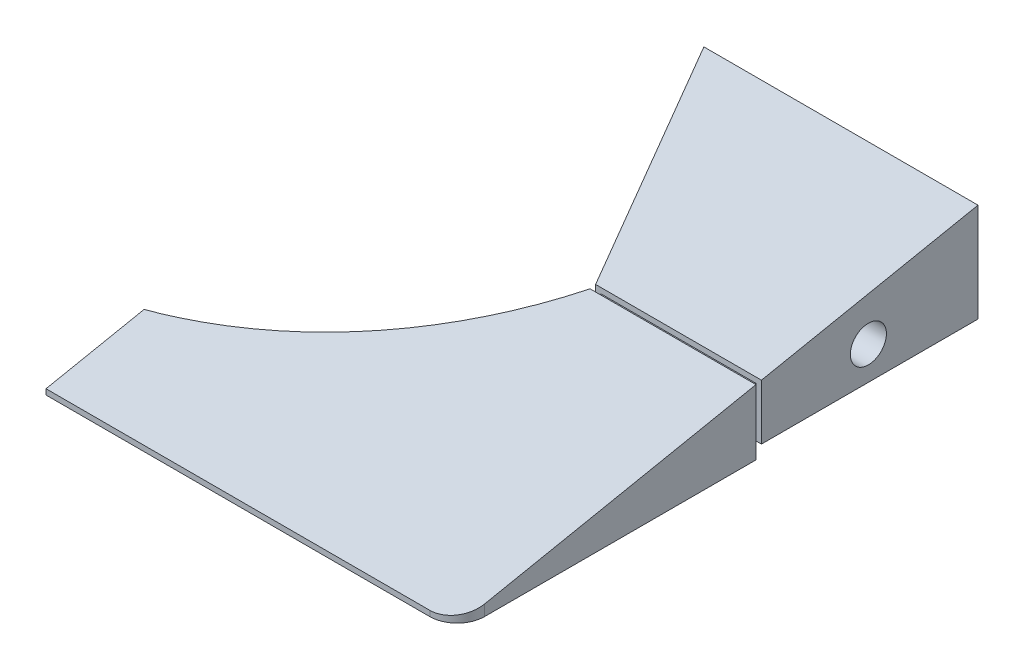
SolidWorks part; units mm, degrees
material "AISI 1020"
ref_plane "Plano frontal" through (0, 0, 0) normal (0, 0, 1) x (1, 0, 0)
ref_plane "Plano superior" through (0, 0, 0) normal (0, 1, 0) x (1, 0, 0)
ref_plane "Plano direito" through (0, 0, 0) normal (1, 0, 0) x (0, 0, -1)
sketch "Esboço1" plane through (0, 0, 0) normal (0, 0, 1) x (1, 0, 0)
  line L1 (-65, 10) -> (65, 10)
  line L2 (-65, 10) -> (-65, -10)
  line L3 (-65, -10) -> (65, -10)
  line L4 (65, 10) -> (65, -10)
  line L5 (-65, 10) -> (65, -10) construction
  line L6 (-65, -10) -> (65, 10) construction
  point P0 (0, 0)
  dimension "D1" = 130
  dimension "D2" = 20
extrude "Ressalto-extrusão1" add sketch "Esboço1" along normal blind 95
sketch "Esboço2" plane through (0, 10, 0) normal (0, 1, 0) x (1, 0, 0)
  line L0 (15, 0) -> (-65, 0)
  line L2 (65, -95) -> (65, 0) construction
  line L3 (35, -40) -> (15, 0)
  line L8 (65, 0) -> (-65, 0) construction
  line L10 (-65, -80) -> (-30.4, -80)
  line L11 (-65, -95) -> (-65, 0) construction
  line L12 (-65, 0) -> (-65, -80)
  arc A0 (-30.4, -80) -> (35, -40) centre (-30.4034, -6.53) ccw
  dimension "D3" = 15
  dimension "D5" = 73.47
  dimension "D1" = 50
  dimension "D2" = 30
  dimension "D4" = 40
extrude "Corte-extrusão2" cut sketch "Esboço2" against normal up to next contours A0 L3 L0 L12 L10
sketch "Esboço3" plane through (65, 0, 0) normal (1, 0, 0) x (0, 0, -1)
  line L0 (0, 10) -> (-95, -9)
  line L1 (-95, -10) -> (-95, 10) construction
  dimension "D1" = 1
extrude "Corte-extrusão3" cut sketch "Esboço3" against normal through all and the other way through all flip side to cut
hole_wizard "Broca de rosquear de cano para tarraxa de 1/82" positions "Esboço7" profile "Esboço8" hole size "1/8" standard "Ansi Inch"
sketch "Esboço7" plane through (65, 0, 0) normal (1, 0, 0) x (0, 0, -1)
  line L0 (0, -10) -> (0, 10) construction
  line L1 (-95, -10) -> (0, -10) construction
  point P0 (-20, -1.945)
  dimension "D1" = 20
  dimension "D2" = 8.055
sketch "Esboço8" plane through (65, -1.945, 20) normal (0, 1, 0) x (0, 0, -1)
  line L0 (0, 0) -> (0, 11.9768)
  line L1 (0, 11.9768) -> (3.29, 10)
  line L2 (3.29, 10) -> (3.29, 0)
  line L5 (3.29, 0) -> (0, 0)
  line L10 (0, 11.9768) -> (-3.29, 10) construction
  line L11 (0, -6.35) -> (0, 107.95) construction
  dimension "Hole Dia." = 6.58
  dimension "Hole Depth" = 10
  dimension "Drill Angle" = 118
hole_wizard "Broca de rosquear de cano para tarraxa de 1/83" positions "Esboço10" profile "Esboço11" hole size "1/8" standard "Ansi Inch"
sketch "Esboço10" plane through (12, 0, -6) normal (-0.8944, 0, 0.4472) x (0.4472, 0, 0.8944)
  line L0 (6.7082, -10) -> (6.7082, 10) construction
  line L1 (6.7082, -10) -> (51.4296, -10) construction
  point P0 (26.7082, -1.945)
  dimension "D1" = 20
  dimension "D2" = 8.055
sketch "Esboço11" plane through (23.9443, -1.945, 17.8885) normal (0, 1, 0) x (0.4472, 0, 0.8944)
  line L0 (0, 0) -> (0, 11.9768)
  line L1 (0, 11.9768) -> (3.29, 10)
  line L2 (3.29, 10) -> (3.29, 0)
  line L5 (3.29, 0) -> (0, 0)
  line L10 (0, 11.9768) -> (-3.29, 10) construction
  line L11 (0, -6.35) -> (0, 107.95) construction
  dimension "Hole Dia." = 6.58
  dimension "Hole Depth" = 10
  dimension "Drill Angle" = 118
fillet "Filete2" radius 5 1 edges at (65, -9.5, 95)
sketch "Esboço14" plane through (65, 0, 0) normal (1, 0, 0) x (0, 0, -1)
  line L0 (-40.5, -10) -> (-39.5, -10)
  line L1 (-90, -10) -> (0, -10) construction
  line L2 (-39.5, -10) -> (-39.5, 2.1)
  line L3 (0, 10) -> (-90, -8) construction
  line L4 (-39.5, 2.1) -> (-40.5, 1.9)
  line L5 (-40.5, 1.9) -> (-40.5, -10)
  dimension "D1" = 1
extrude "Corte-extrusão5" cut sketch "Esboço14" against normal through all
sketch "Esboço15" plane through (0, 0, 39.5) normal (0, 0, 1) x (1, 0, 0)
  line L0 (34.75, 2.1) -> (65, 2.1) construction
  line L1 (35.75, 1.1) -> (64, 1.1)
  line L2 (35.75, 1.1) -> (35.75, -7)
  line L3 (35.75, -7) -> (64, -7)
  line L4 (64, 1.1) -> (64, -7)
  line L5 (65, -10) -> (65, 2.1) construction
  line L6 (34.75, -10) -> (34.75, 2.1) construction
  line L8 (34.75, -10) -> (65, -10) construction
  dimension "D1" = 1
  dimension "D2" = 1
  dimension "D3" = 1
  dimension "D4" = 3
extrude "Ressalto-extrusão2" add sketch "Esboço15" along normal up to next
sketch "Esboço16" plane through (0, 0, 0) normal (0, 0, -1) x (-1, 0, 0)
  line L0 (-65, -10) -> (-65, -8)
  line L2 (-65, -8) -> (-15, -8)
  line L3 (-15, -10) -> (-15, 10) construction
  line L4 (-15, -8) -> (-15, -10)
  line L5 (-34.7417, -10) -> (30.4, -10) construction
  line L6 (-15, -10) -> (-65, -10)
  point P5 (0, 0)
  point P12 (0, 0)
  dimension "D1" = 2
extrude "Corte-extrusão6" cut sketch "Esboço16" against normal blind 40.5
sketch "Esboço17" plane through (0, 9.6154, 1.9231) normal (0, 0.9806, 0.1961) x (1, 0, 0)
  line L0 (-10, -76.676) -> (-10, -96.2978)
  line L2 (-10, -96.2978) -> (-65, -96.2978)
  line L3 (-65, -96.2978) -> (-65, -76.676)
  line L4 (-65, -76.676) -> (-10, -76.676)
  line L5 (65, -39.3409) -> (65, -89.8212) construction
  ellipse E0 centre (-30.4034, -4.6982) end of major axis (-30.4034, 70.2268) minor radius 73.47 (-30.4, -79.6232) -> (34.7417, -39.3409) ccw construction
  dimension "D1" = 75
extrude "Corte-extrusão7" cut sketch "Esboço17" against normal up to next contours L2 L3 L4 L0
